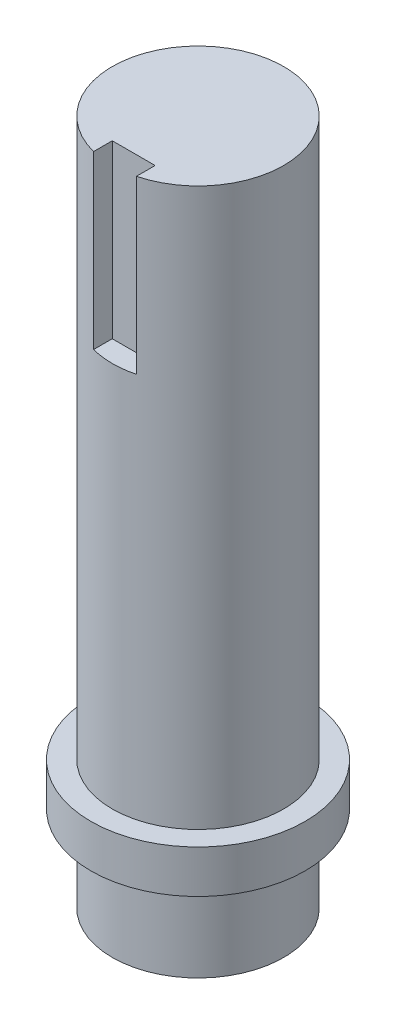
SolidWorks part; units mm, degrees
ref_plane "Front Plane" through (0, 0, 0) normal (0, 0, 1) x (1, 0, 0)
ref_plane "Top Plane" through (0, 0, 0) normal (0, 1, 0) x (1, 0, 0)
ref_plane "Right Plane" through (0, 0, 0) normal (1, 0, 0) x (0, 0, -1)
sketch "Sketch1" plane through (0, 0, 0) normal (0, 1, 0) x (1, 0, 0)
  circle A0 centre (0, 0) radius 15.875
  dimension "D1" = 31.75
extrude "Boss-Extrude1" add sketch "Sketch1" along normal blind 101.6
sketch "Sketch2" plane through (0, 101.6, 0) normal (0, 1, 0) x (1, 0, 0)
  circle A0 centre (0, 0) radius 12.7
  dimension "D1" = 25.4
extrude "Cut-Extrude1" cut sketch "Sketch2" against normal blind 82.55 flip side to cut
sketch "Sketch3" plane through (0, 101.6, 0) normal (0, 1, 0) x (1, 0, 0)
  line L1 (-3.175, -15.875) -> (3.175, -15.875)
  line L2 (-3.175, -15.875) -> (-3.175, -9.525)
  line L3 (-3.175, -9.525) -> (3.175, -9.525)
  line L4 (3.175, -15.875) -> (3.175, -9.525)
  line L5 (-3.175, -15.875) -> (3.175, -9.525) construction
  line L6 (-3.175, -9.525) -> (3.175, -15.875) construction
  circle A0 centre (0, 0) radius 12.7 construction
  point P0 (0, -12.7)
  dimension "D1" = 6.35
  dimension "D2" = 6.35
extrude "Cut-Extrude2" cut sketch "Sketch3" against normal blind 25.4
sketch "Sketch4" plane through (0, 0, 0) normal (0, -1, 0) x (1, 0, 0)
  circle A0 centre (0, 0) radius 12.7
  dimension "D1" = 25.4
extrude "Cut-Extrude3" cut sketch "Sketch4" against normal blind 12.7 flip side to cut
